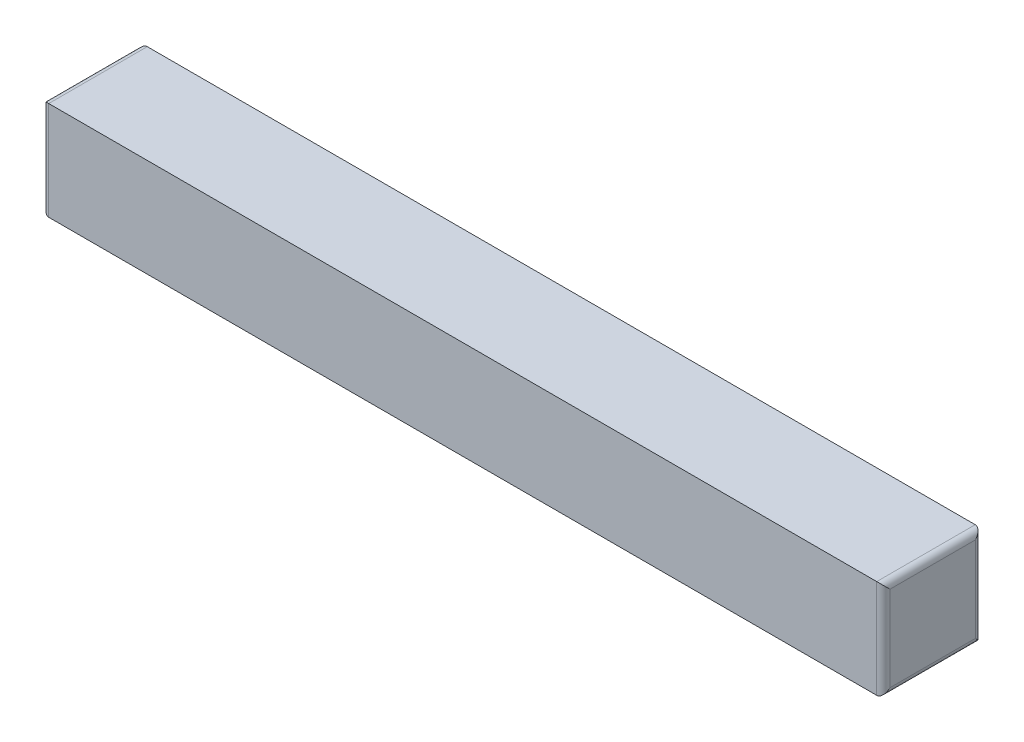
SolidWorks part; units mm, degrees
ref_plane "Front Plane" through (0, 0, 0) normal (0, 0, 1) x (1, 0, 0)
ref_plane "Top Plane" through (0, 0, 0) normal (0, 1, 0) x (1, 0, 0)
ref_plane "Right Plane" through (0, 0, 0) normal (1, 0, 0) x (0, 0, -1)
sketch "Sketch1" plane through (0, 0, 0) normal (0, 0, 1) x (1, 0, 0)
  line L1 (0, 0) -> (25.4, 0)
  line L2 (0, 0) -> (0, 2.975)
  line L3 (0, 2.975) -> (25.4, 2.975)
  line L4 (25.4, 0) -> (25.4, 2.975)
  dimension "D1" = 25.4
  dimension "D2" = 2.975
extrude "Boss-Extrude1" add sketch "Sketch1" along normal blind 2.975
fillet "Fillet2" radius 0.2 8 edges at (25.4, 1.4875, 0) (25.4, 0, 1.4875) (25.4, 1.4875, 2.975) (25.4, 2.975, 1.4875) (0, 1.4875, 0) (0, 0, 1.4875) (0, 1.4875, 2.975) (0, 2.975, 1.4875)
